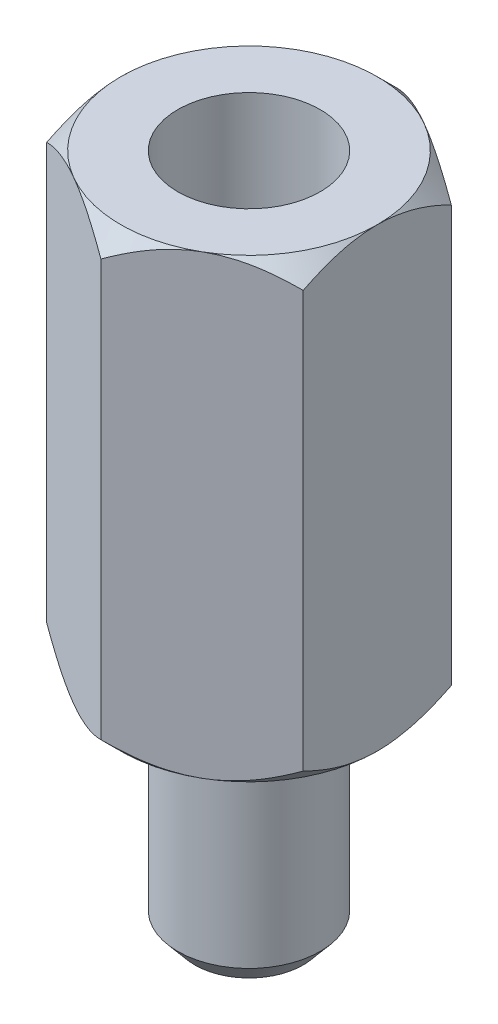
SolidWorks part; units mm, degrees
ref_plane "Front Plane" through (0, 0, 0) normal (0, 0, 1) x (1, 0, 0)
ref_plane "Top Plane" through (0, 0, 0) normal (0, 1, 0) x (1, 0, 0)
ref_plane "Right Plane" through (0, 0, 0) normal (1, 0, 0) x (0, 0, -1)
sketch "Sketch1" plane through (0, 0, 0) normal (0, 1, 0) x (1, 0, 0)
  circle A0 centre (0, 0) radius 1.25
  dimension "D1" = 2.5
extrude "Boss-Extrude1" add sketch "Sketch1" along normal blind 3.9
sketch "Sketch2" plane through (0, 3.9, 0) normal (0, 1, 0) x (1, 0, 0)
  line L1 (0, 2.5981) -> (-2.25, 1.299)
  line L2 (-2.25, 1.299) -> (-2.25, -1.299)
  line L3 (-2.25, -1.299) -> (0, -2.5981)
  line L4 (0, -2.5981) -> (2.25, -1.299)
  line L5 (2.25, -1.299) -> (2.25, 1.299)
  line L6 (2.25, 1.299) -> (0, 2.5981)
  circle A0 centre (0, 0) radius 2.25 construction
  dimension "D1" = 4.5
extrude "Boss-Extrude2" add sketch "Sketch2" along normal blind 8
sketch "Sketch3" plane through (0, 11.9, 0) normal (0, 1, 0) x (1, 0, 0)
  circle A0 centre (0, 0) radius 1.25
  dimension "D1" = 2.5
extrude "Cut-Extrude2" cut sketch "Sketch3" against normal blind 4.8
sketch "Sketch4" plane through (0, 11.9, 0) normal (0, 1, 0) x (1, 0, 0)
  circle A0 centre (0, 0) radius 2.25
extrude "Cut-Extrude3" cut sketch "Sketch4" against normal through all draft 45 flip side to cut
sketch "Sketch5" plane through (0, 3.9, 0) normal (0, -1, 0) x (1, 0, 0)
  circle A0 centre (0, 0) radius 2.25
extrude "Cut-Extrude6" cut sketch "Sketch5" against normal through all draft 45 flip side to cut
chamfer "Chamfer2" distance 0.3 angle 50 1 edges at (0, 0, 1.25)
